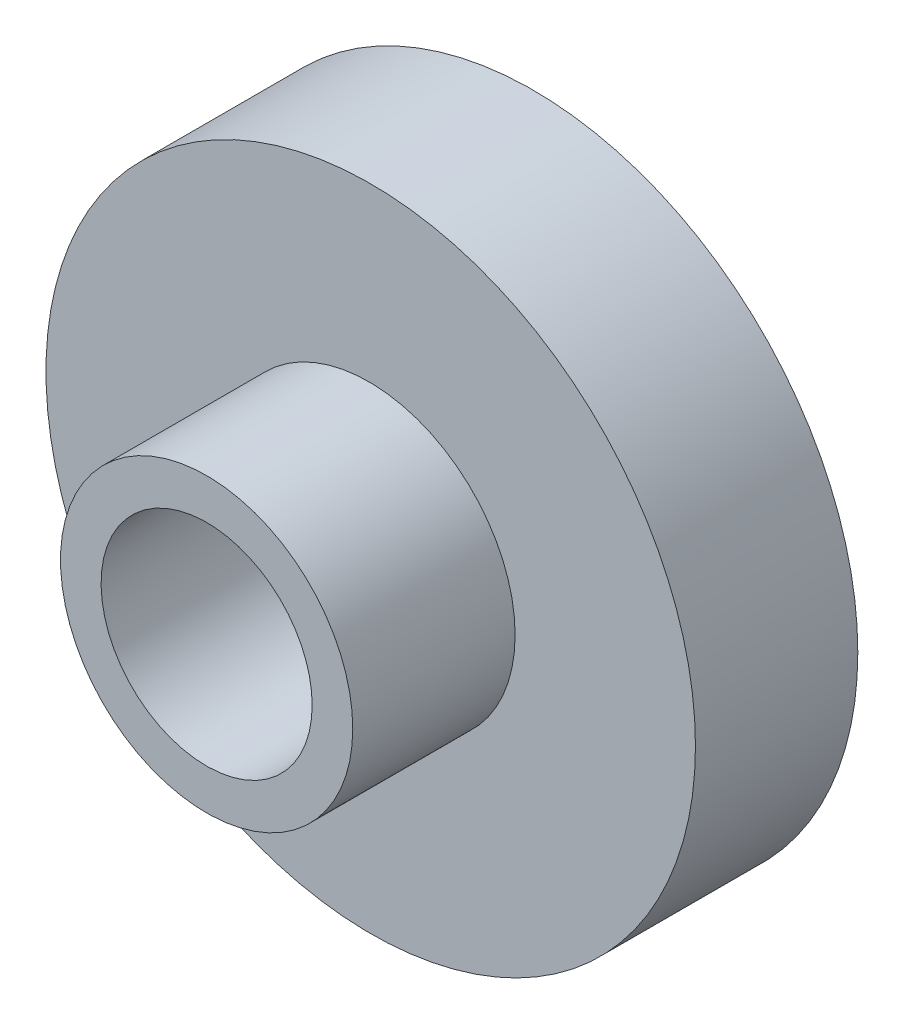
SolidWorks part; units mm, degrees
ref_plane "Front Plane" through (0, 0, 0) normal (0, 0, 1) x (1, 0, 0)
ref_plane "Top Plane" through (0, 0, 0) normal (0, 1, 0) x (1, 0, 0)
ref_plane "Right Plane" through (0, 0, 0) normal (1, 0, 0) x (0, 0, -1)
sketch "Sketch1" plane through (0, 0, 0) normal (0, 0, 1) x (1, 0, 0)
  circle A0 centre (0, 0) radius 10
  dimension "D1" = 20
extrude "Boss-Extrude2" add sketch "Sketch1" along normal blind 5
sketch "Sketch2" plane through (0, 0, 5) normal (0, 0, 1) x (1, 0, 0)
  circle A2 centre (-0.0531, 0.1934) radius 4.5
  circle A3 centre (-0.0531, 0.1934) radius 3.25
  point P3 (0, 0)
extrude "Boss-Extrude3" add sketch "Sketch2" along normal blind 5
sketch "Sketch3" plane through (0, 0, 5) normal (0, 0, 1) x (1, 0, 0)
  circle A0 centre (0, 0) radius 3.4506
extrude "Cut-Extrude1" cut sketch "Sketch3" against normal blind 5
